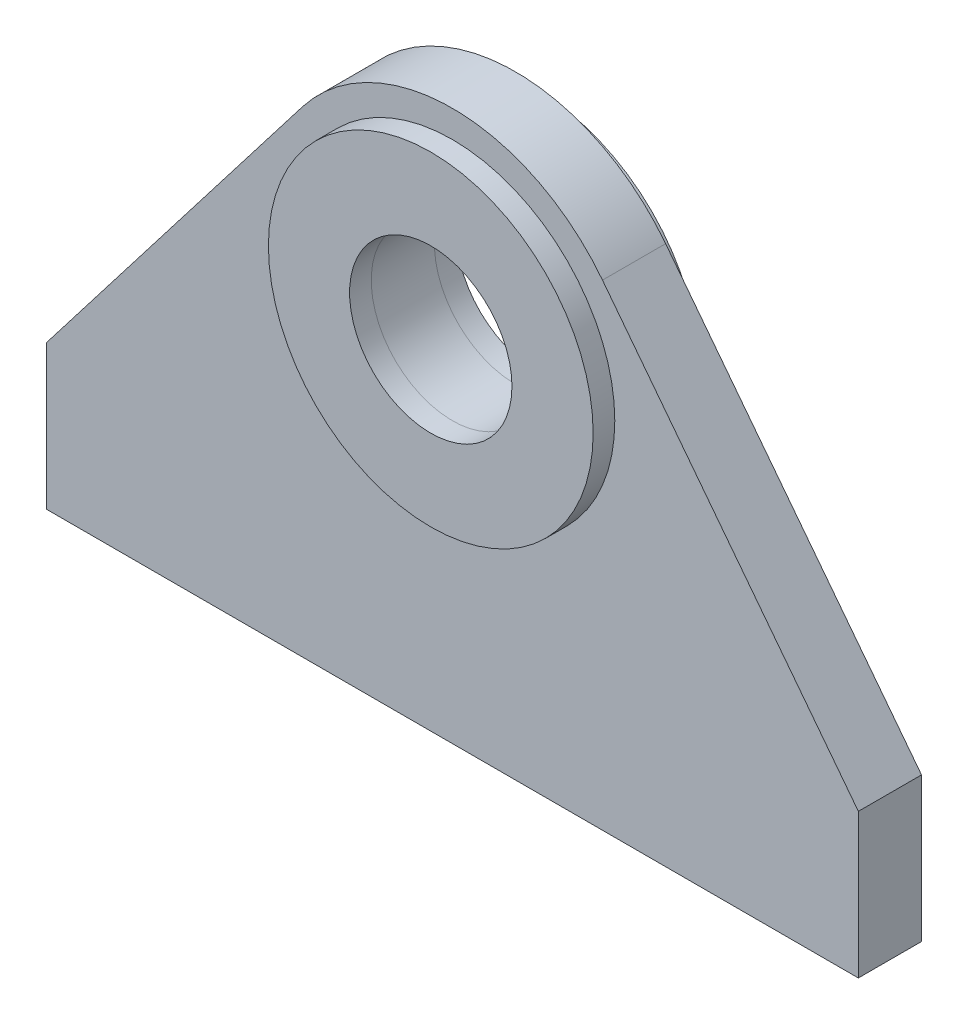
SolidWorks part; units mm, degrees
material "S235J0"
ref_plane "Front Plane" through (0, 0, 0) normal (0, 0, 1) x (1, 0, 0)
ref_plane "Top Plane" through (0, 0, 0) normal (0, 1, 0) x (1, 0, 0)
ref_plane "Right Plane" through (0, 0, 0) normal (1, 0, 0) x (0, 0, -1)
sketch "Sketch1" plane through (0, 0, 0) normal (0, 0, 1) x (1, 0, 0)
  line L0 (-225, 0) -> (225, 0)
  line L1 (-225, 0) -> (-225, 80)
  line L2 (-225, 80) -> (-83.1772, 264.0823)
  line L3 (0, 0) -> (0, 74.1415) construction
  line L4 (225, 0) -> (225, 80)
  line L5 (225, 80) -> (83.1772, 264.0823)
  arc A0 (83.1772, 264.0823) -> (-83.1772, 264.0823) centre (0, 200) ccw
  circle A1 centre (0, 200) radius 45
  point P5 (0, 0)
  dimension "D1" = 210
  dimension "D3" = 90
  dimension "D5" = 200
  dimension "D2" = 450
  dimension "D4" = 80
extrude "Boss-Extrude1" add sketch "Sketch1" along normal mid plane 35
sketch "Sketch2" plane through (0, 0, 17.5) normal (0, 0, 1) x (1, 0, 0)
  circle A0 centre (0, 200) radius 90
  arc A1 (83.1772, 264.0823) -> (-83.1772, 264.0823) centre (0, 200) ccw construction
  circle A2 centre (0, 200) radius 45 construction
  circle A3 centre (0, 200) radius 45
  dimension "D1" = 15
extrude "Boss-Extrude2" add sketch "Sketch2" along normal blind 12 separate body
mirror "Mirror1" about plane through (0, 0, 0) normal (0, 0, 1) of bodies 102
sketch "Sketch3" plane through (0, 0, 0) normal (0, 0, 1) x (1, 0, 0)
  line L0 (0, 390.4678) -> (0, -81.4946) construction
  line L1 (-256.3856, 200) -> (256.3856, 200) construction
  line L2 (0, 200) -> (196.4941, 396.4941) construction
  point P5 (0, 200)
  dimension "D1" = 45
sketch3d "3DSketch1"
  line L0 (0, 200, 0) -> (0, 200, 256.3856) construction
  line L1 (-256.3856, 200, 0) -> (256.3856, 200, 0) construction
  line L2 (0, 200, 0) -> (0, 200, -256.3856) construction
  line L3 (-256.3856, 200, 0) -> (-256.3856, 200, 256.3856) construction
  line L4 (-256.3856, 200, 256.3856) -> (0, 200, 256.3856) construction
  line L5 (0, 200, 0) -> (-256.3856, 200, 256.3856) construction
  dimension "D1" = 45
sketch "Sketch4" [suppressed] plane through (0, 0, 0) normal (0, 1, 0) x (1, 0, 0)
  line L0 (-500, 500) -> (500, 500)
  line L1 (-500, 500) -> (-500, -500)
  line L2 (500, 500) -> (500, -500)
  line L3 (-500, -500) -> (500, -500)
  point P0 (0, 500)
  point P3 (-500, 0)
  dimension "D1" = 1000
  dimension "D2" = 1000
extrude "Boss-Extrude3" [suppressed] add sketch "Sketch4" against normal blind 20 separate body
sketch "Sketch5" [suppressed] plane through (225, 0, 0) normal (1, 0, 0) x (0, 0, -1)
  line L0 (-17.5, 25) -> (-37.5, 0)
  line L1 (-17.5, 0) -> (-17.5, 80) construction
  line L2 (-500, 0) -> (500, 0) construction
  line L3 (-37.5, 0) -> (-17.5, 0)
  line L4 (-17.5, 0) -> (-17.5, 25)
  line L5 (-17.5, 0) -> (-17.5, 80) construction
  dimension "D1" = 25
  dimension "D2" = 20
sketch "Sketch6" [suppressed] plane through (0, 0, 0) normal (0, 1, 0) x (1, 0, 0)
  line L3 (-225, -17.5) -> (225, -17.5)
  line L6 (-225, -17.5) -> (-225, 17.5) construction
  line L7 (-225, -17.5) -> (225, -17.5) construction
  line L8 (225, -37.5) -> (225, -17.5) construction
  line L9 (225, -17.5) -> (83.1772, -17.5) construction
sweep "Sweep1" [suppressed] add profiles "Sketch5" path "Sketch6"
sketch "Sketch8" [suppressed] plane through (0, 0, 0) normal (1, 0, 0) x (0, 0, -1)
  line L0 (-17.5, 302) -> (-27.5, 290)
  line L1 (-17.5, 305) -> (-17.5, 264.0823) construction
  line L2 (-27.5, 290) -> (-17.5, 290)
  line L3 (-17.5, 290) -> (-17.5, 302)
  line L4 (-17.5, 290) -> (-29.5, 290) construction
  line L5 (-29.5, 200) -> (0, 200) construction
  line L6 (-29.5, 290) -> (-29.5, 110) construction
  dimension "D1" = 12
  dimension "D2" = 10
revolve "Revolve1" [suppressed] add sketch "Sketch8" angle 360 about L5
mirror "Mirror2" [suppressed] about plane through (0, 0, 0) normal (0, 0, 1)
mirror "Mirror3" [suppressed] about plane through (0, 0, 0) normal (0, 0, 1)
